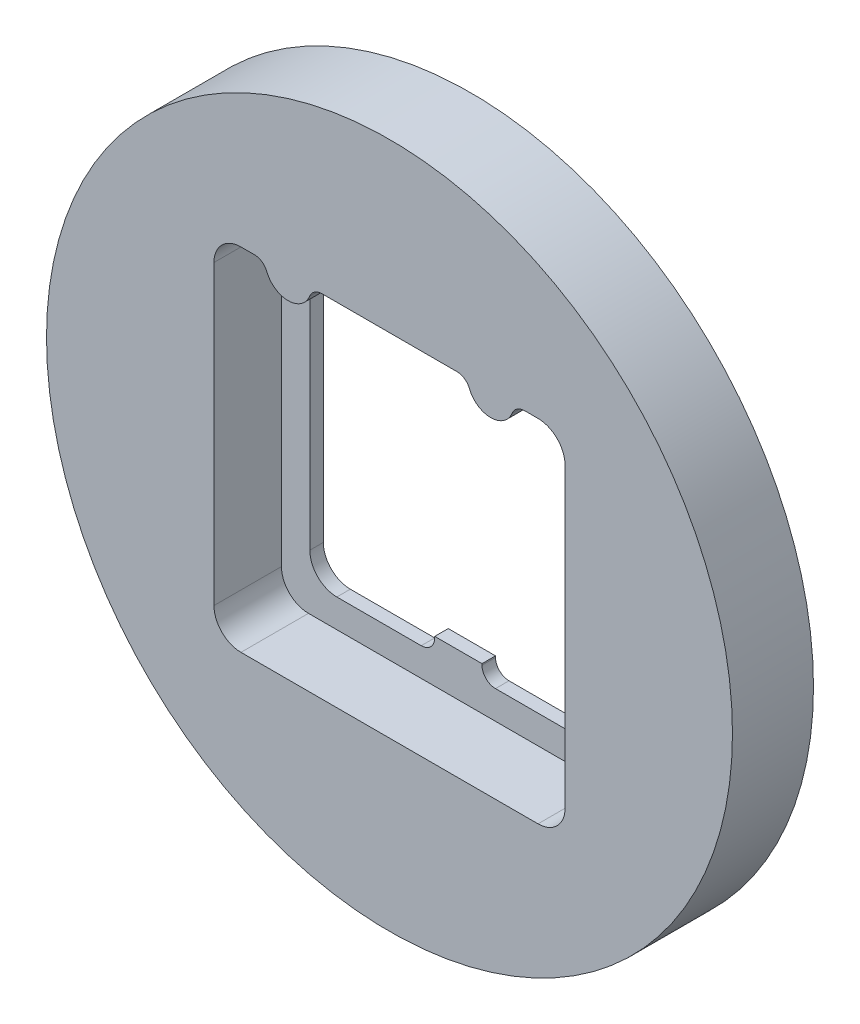
SolidWorks part; units mm, degrees
ref_plane "Front Plane" through (0, 0, 0) normal (0, 0, 1) x (1, 0, 0)
ref_plane "Top Plane" through (0, 0, 0) normal (0, 1, 0) x (1, 0, 0)
ref_plane "Right Plane" through (0, 0, 0) normal (1, 0, 0) x (0, 0, -1)
sketch "Sketch1" plane through (0, 0, 0) normal (0, 0, 1) x (1, 0, 0)
  circle A0 centre (0, 0) radius 25.4
  dimension "D1" = 50.8
extrude "Boss-Extrude1" add sketch "Sketch1" along normal blind 6
sketch "Sketch2" plane through (0, 0, 6) normal (0, 0, 1) x (1, 0, 0)
  line L0 (-11, -9) -> (-11, 9)
  line L1 (-11, -13) -> (11, -13)
  line L2 (-13, -11) -> (-13, 11)
  line L3 (-11, 13) -> (-10.008, 13)
  line L4 (13, -11) -> (13, 11)
  line L5 (-13, -13) -> (13, 13) construction
  line L6 (-13, 13) -> (13, -13) construction
  line L7 (-9, 11) -> (9, 11)
  line L8 (11, -9) -> (11, 9)
  line L9 (-9, -11) -> (-2.75, -11)
  line L10 (-13, -13) -> (13, -13) construction
  line L11 (13, -13) -> (13, 13) construction
  line L12 (-13, 13) -> (13, 13) construction
  line L13 (-13, -13) -> (-13, 13) construction
  line L14 (-11, -11) -> (-11, 11) construction
  line L15 (-11, -11) -> (11, -11) construction
  line L16 (11, -11) -> (11, 11) construction
  line L17 (-11, 11) -> (11, 11) construction
  line L18 (0, 16.8218) -> (0, -19.7341) construction
  line L19 (2.75, -11) -> (9, -11)
  line L20 (-1.75, -9.9) -> (1.75, -9.9)
  line L21 (-1.75, -9.9) -> (-1.75, -10)
  line L23 (1.75, -9.9) -> (1.75, -10)
  line L24 (-1.75, -9.9) -> (1.75, -11) construction
  line L25 (-1.75, -11) -> (1.75, -9.9) construction
  line L26 (-7.5, 15.5477) -> (-7.5, -17.7926) construction
  line L27 (-4.992, 13) -> (4.992, 13)
  line L28 (7.5, 16.6357) -> (7.5, 0.1568) construction
  line L29 (10.008, 13) -> (11, 13)
  arc A0 (11, -13) -> (13, -11) centre (11, -11) ccw
  arc A1 (11, 13) -> (13, 11) centre (11, 11) cw
  arc A2 (-13, 11) -> (-11, 13) centre (-11, 11) cw
  arc A3 (-11, -13) -> (-13, -11) centre (-11, -11) cw
  arc A4 (-11, -9) -> (-9, -11) centre (-9, -9) ccw
  arc A5 (11, -9) -> (9, -11) centre (9, -9) cw
  arc A6 (9, 11) -> (11, 9) centre (9, 9) cw
  arc A7 (-11, 9) -> (-9, 11) centre (-9, 9) cw
  arc A8 (2.75, -11) -> (1.75, -10) centre (2.75, -10) cw
  arc A9 (-1.75, -10) -> (-2.75, -11) centre (-2.75, -10) cw
  arc A10 (-9.0791, 12.3704) -> (-5.9209, 12.3704) centre (-7.5, 13) ccw
  arc A11 (-10.008, 13) -> (-9.0791, 12.3704) centre (-10.008, 12) cw
  arc A12 (5.9209, 12.3704) -> (9.0791, 12.3704) centre (7.5, 13) ccw
  arc A13 (5.9209, 12.3704) -> (4.992, 13) centre (4.992, 12) ccw
  arc A14 (9.0791, 12.3704) -> (10.008, 13) centre (10.008, 12) cw
  arc A15 (-5.9209, 12.3704) -> (-4.992, 13) centre (-4.992, 12) cw
  point P0 (0, 0)
  point P36 (0, -10.45)
  point P63 (9.2, 13)
  point P66 (-5.8, 13)
  dimension "D4" = 2
  dimension "D6" = 1
  dimension "D9" = 3.4
  dimension "D10" = 1
  dimension "D12" = 3.4
  dimension "D13" = 1
  dimension "D14" = 1
  dimension "D1" = 26
  dimension "D2" = 26
  dimension "D5" = 3.5
  dimension "D7" = 1.1
  dimension "D8" = 5.5
  dimension "D11" = 5.5
  dimension "D3" = 2
extrude "Cut-Extrude2" cut sketch "Sketch2" against normal blind 5 contours A15 A10 A11 L3 A2 L2 A3 L1 A0 L4 A1 L29 A14 A12 A13 L27
sketch "Sketch3" plane through (0, 0, 1) normal (0, 0, 1) x (1, 0, 0)
  line L0 (-10.9, -8.9) -> (-10.9, 9.1)
  line L1 (-8.9, 11.1) -> (9.1, 11.1)
  line L2 (11.1, -8.9) -> (11.1, 9.1)
  line L3 (-8.9, -10.9) -> (-2.65, -10.9)
  line L4 (2.85, -10.9) -> (9.1, -10.9)
  line L5 (-1.65, -9.8) -> (1.85, -9.8)
  line L6 (-1.65, -9.8) -> (-1.65, -9.9)
  line L7 (1.85, -9.8) -> (1.85, -9.9)
  line L8 (13, -11) -> (13, 11) construction
  line L9 (-4.992, 13) -> (4.992, 13) construction
  arc A0 (-10.9, -8.9) -> (-8.9, -10.9) centre (-8.9, -8.9) ccw
  arc A1 (11.1, -8.9) -> (9.1, -10.9) centre (9.1, -8.9) cw
  arc A2 (9.1, 11.1) -> (11.1, 9.1) centre (9.1, 9.1) cw
  arc A3 (-10.9, 9.1) -> (-8.9, 11.1) centre (-8.9, 9.1) cw
  arc A4 (2.85, -10.9) -> (1.85, -9.9) centre (2.85, -9.9) cw
  arc A5 (-1.65, -9.9) -> (-2.65, -10.9) centre (-2.65, -9.9) cw
  dimension "D1" = 1.9
  dimension "D2" = 1.9
extrude "Cut-Extrude3" cut sketch "Sketch3" against normal through all
